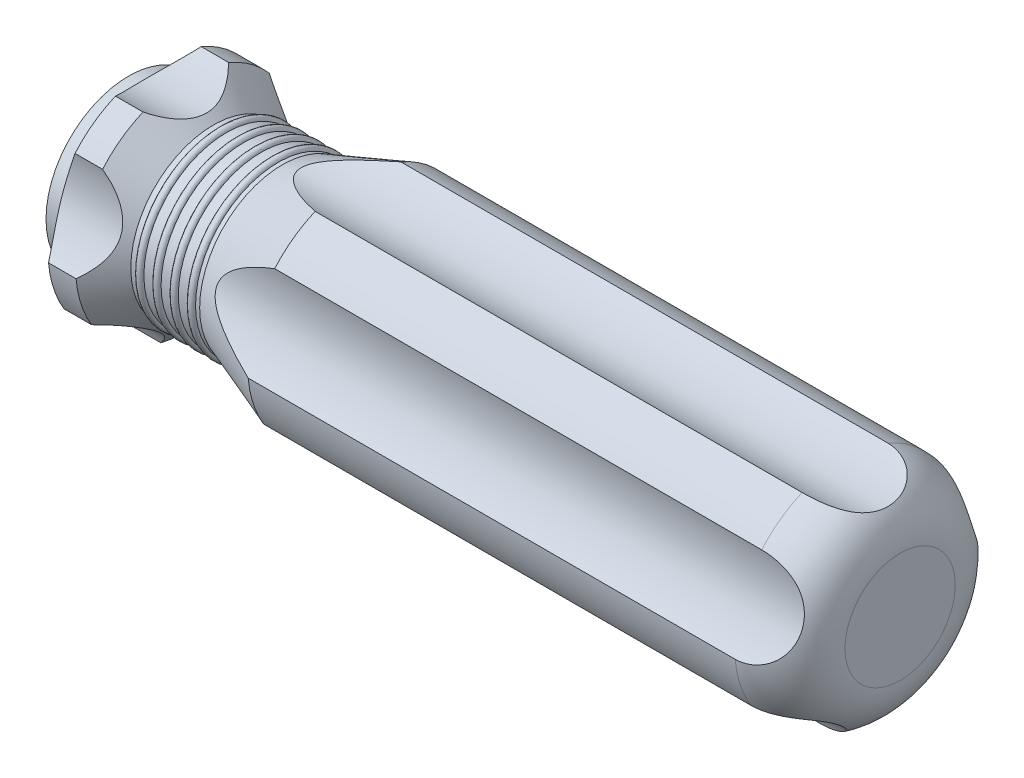
SolidWorks part; units mm, degrees
ref_plane "Front Plane" through (0, 0, 0) normal (0, 0, 1) x (1, 0, 0)
ref_plane "Top Plane" through (0, 0, 0) normal (0, 1, 0) x (1, 0, 0)
ref_plane "Right Plane" through (0, 0, 0) normal (1, 0, 0) x (0, 0, -1)
sketch "Sketch1" plane through (0, 0, 0) normal (0, 0, 1) x (1, 0, 0)
  line L0 (0, 6) -> (1, 6)
  line L1 (0, 0) -> (56, 0)
  line L2 (0, 0) -> (0, 8) construction
  line L3 (0, 8) -> (2.1547, 8) construction
  line L4 (56, 0) -> (56, 4)
  line L5 (1, 6) -> (2.1547, 8)
  line L6 (2.1547, 8) -> (4.1547, 8) construction
  line L7 (4.1547, 8) -> (6.1547, 6)
  line L8 (6.1547, 6) -> (11.1547, 6)
  line L9 (11.1547, 6) -> (16.6497, 8)
  line L10 (4.1547, 8) -> (56, 8) construction
  line L11 (2.1547, 8) -> (4.1547, 8)
  line L12 (16.6497, 8) -> (52, 8)
  line L13 (0, 6) -> (0, 0)
  arc A0 (52, 8) -> (56, 4) centre (52, 4) cw
  dimension "D10" = 4
  dimension "D1" = 56
  dimension "D2" = 8
  dimension "D3" = 1
  dimension "D4" = 120
  dimension "D5" = 2
  dimension "D6" = 2
  dimension "D7" = 5
  dimension "D8" = 135
  dimension "D9" = 20
revolve "Revolve1" add sketch "Sketch1" angle 360 about L1
sketch "Sketch2" plane through (0, 0, 0) normal (0, 0, 1) x (1, 0, 0)
  line L0 (11.1547, 6) -> (6.1547, 6) construction
  line L1 (6.1547, 6) -> (6.1547, -6) construction
  line L2 (0, 0) -> (56, 0) construction
  line L3 (56, -4) -> (56, 4) construction
  circle A0 centre (6.8547, 6) radius 0.25
  dimension "D1" = 0.5
  dimension "D2" = 0.7
revolve "Revolve2" add sketch "Sketch2" angle 360 about L2
pattern_linear "LPattern1" count 4 spacing 1.25 along (1, 0, 0) of "Revolve2"
sketch "Sketch3" plane through (0, 0, 0) normal (-1, 0, 0) x (0, 0, 1)
  circle A0 centre (0, 12.5) radius 6
  dimension "D1" = 12
  dimension "D2" = 12.5
extrude "Cut-Extrude1" cut sketch "Sketch3" against normal through all
pattern_circular "CirPattern1" count 5 over 360 about axis through (0, 0, 0) along (1, 0, 0) of "Cut-Extrude1"
sketch "Sketch4" plane through (0, 0, 0) normal (-1, 0, 0) x (0, 0, 1)
  circle A0 centre (0, 0) radius 1.5
  dimension "D1" = 3
extrude "Cut-Extrude2" cut sketch "Sketch4" against normal blind 30
